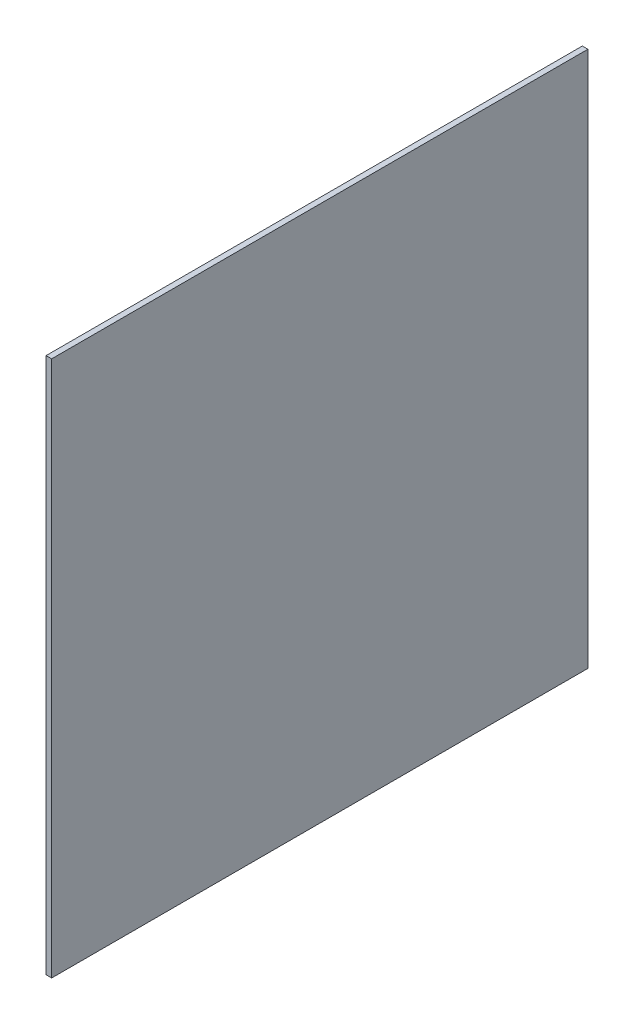
SolidWorks part; units mm, degrees
material "ASTM A36 Steel"
ref_plane "Front Plane" through (0, 0, 0) normal (0, 0, 1) x (1, 0, 0)
ref_plane "Top Plane" through (0, 0, 0) normal (0, 1, 0) x (1, 0, 0)
ref_plane "Right Plane" through (0, 0, 0) normal (1, 0, 0) x (0, 0, -1)
sketch "Sketch1" plane through (0, 0, 0) normal (1, 0, 0) x (0, 0, -1)
  line L1 (152.4, 152.4) -> (-152.4, 152.4)
  line L2 (152.4, 152.4) -> (152.4, -152.4)
  line L3 (152.4, -152.4) -> (-152.4, -152.4)
  line L4 (-152.4, 152.4) -> (-152.4, -152.4)
  line L5 (152.4, 152.4) -> (-152.4, -152.4) construction
  line L6 (152.4, -152.4) -> (-152.4, 152.4) construction
  point P0 (0, 0)
  dimension "D1" = 304.8
  dimension "D2" = 304.8
extrude "Boss-Extrude1" add sketch "Sketch1" along normal mid plane 3.175
